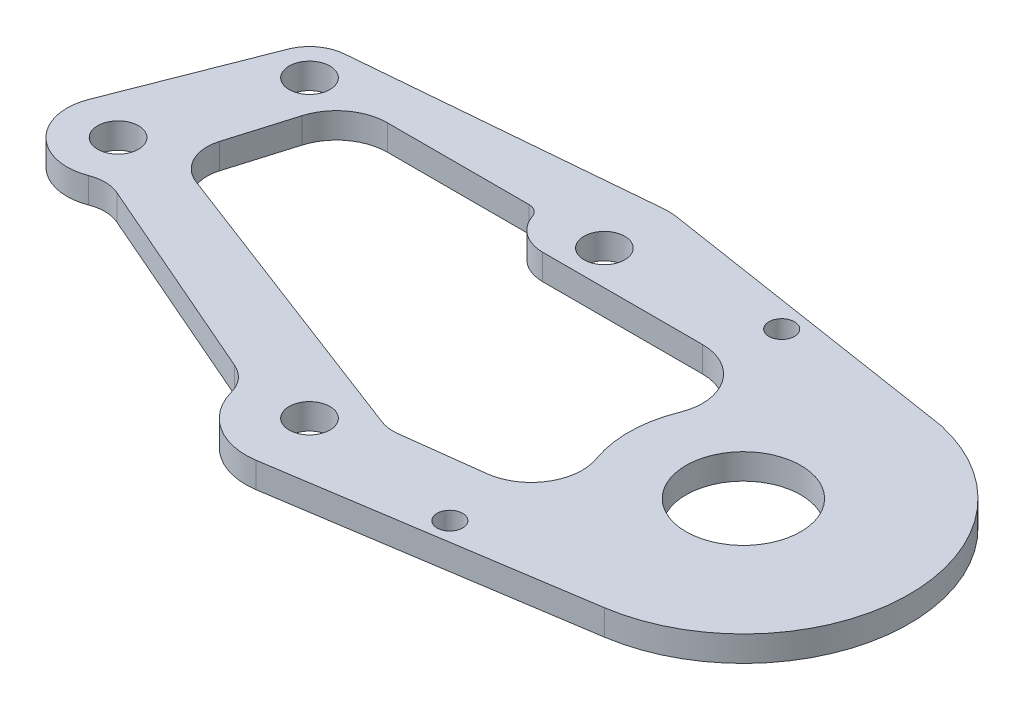
SolidWorks part; units mm, degrees
ref_plane "Front Plane" through (0, 0, 0) normal (0, 0, 1) x (1, 0, 0)
ref_plane "Top Plane" through (0, 0, 0) normal (0, 1, 0) x (1, 0, 0)
ref_plane "Right Plane" through (0, 0, 0) normal (1, 0, 0) x (0, 0, -1)
sketch "Sketch1" plane through (0, 0, 0) normal (0, 1, 0) x (1, 0, 0)
  line L1 (35.9792, -12.8485) -> (12.3136, -16.494)
  line L3 (36.8136, 12.6919) -> (12.3191, 16.493)
  line L5 (11.1196, 16.5334) -> (-11.812, 14.5411)
  line L7 (-14.2449, 12.8753) -> (-19.4876, 2.2049)
  line L9 (-16.9948, -4.5849) -> (9.5576, -16.1371)
  circle A0 centre (0, 0) radius 5.5
  circle A9 centre (-15, 0) radius 1.6
  circle A12 centre (14, 0) radius 4.5
  circle A20 centre (25, 11) radius 1
  circle A21 centre (25, -11) radius 1
  circle A23 centre (34, 0) radius 4.5
  circle A24 centre (-11.5524, 11.5524) radius 1.6
  circle A25 centre (11.5523, 11.5522) radius 1.6
  circle A26 centre (11.5523, -11.5523) radius 1.6
  arc A33 (12.3191, 16.493) -> (11.1196, 16.5334) centre (11.5523, 11.5522) ccw
  arc A34 (-11.812, 14.5411) -> (-14.2449, 12.8753) centre (-11.5524, 11.5524) ccw
  arc A35 (-19.4876, 2.2049) -> (-16.9948, -4.5849) centre (-15, 0) ccw
  arc A36 (9.5576, -16.1371) -> (12.3136, -16.494) centre (11.5523, -11.5523) ccw
  arc A37 (35.9792, -12.8485) -> (35.1652, 12.9477) centre (34, 0) ccw
extrude "Boss-Extrude2" add sketch "Sketch1" along normal blind 2 contours L1 A37 L3 A33 L5 A34 L7 A35 L9 A36 A0 A9 A12 A20 A21 A23 A24 A25 A26
sketch "Sketch2" plane through (0, 2, 0) normal (0, 1, 0) x (1, 0, 0)
  circle A0 centre (25, 11) radius 1
  circle A1 centre (25, -11) radius 1
extrude "Boss-Extrude3" add sketch "Sketch2" against normal up to surface (2 mm away) up to face at (0, 0, 5.5)
sketch "Sketch3" plane through (0, 2, 0) normal (0, 1, 0) x (1, 0, 0)
  circle A0 centre (24, 13) radius 1
  circle A1 centre (24, -13) radius 1
extrude "Cut-Extrude1" cut sketch "Sketch3" against normal blind 103
sketch "Sketch4" plane through (0, 2, 0) normal (0, 1, 0) x (1, 0, 0)
  line L0 (-11.5562, 1.049) -> (-9.2694, 8.7117)
  line L1 (-9.2694, 8.7117) -> (11.5178, 8.4785)
  line L2 (-11.5562, 1.049) -> (11.5464, -7.7739)
  line L4 (11.5464, -7.7739) -> (15.2588, -9.1916)
  line L5 (11.5178, 8.4785) -> (14.721, 8.4426)
  arc A6 (15.2588, -9.1916) -> (14.721, 8.4426) centre (14.9899, -0.3745) ccw
extrude "Cut-Extrude2" cut sketch "Sketch4" against normal blind 10
sketch "Sketch5" plane through (0, 2, 0) normal (0, 1, 0) x (1, 0, 0)
  line L0 (-5.3378, -1.3258) -> (3.0952, -4.5464)
  line L1 (3.0952, -4.5464) -> (3.756, -8.1059)
  line L2 (3.756, -8.1059) -> (-7.7705, -5.6439)
  line L3 (-7.7705, -5.6439) -> (-5.3378, -1.3258)
extrude "Boss-Extrude4" add sketch "Sketch5" against normal up to surface (2 mm away) up to face at (2.4813, 0, -0.201)
fillet "Fillet1" radius 3 4 edges at (14.721, 1, -8.4426) (15.2588, 1, 9.1916) (-9.2694, 1, -8.7117) (-11.5562, 1, -1.049)
sketch "Sketch6" plane through (0, 2, 0) normal (0, 1, 0) x (1, 0, 0)
  line L0 (-10.4151, -1.9948) -> (6.9675, -9.5575)
  line L2 (-16.9948, -4.5849) -> (-19.442, -14.3186)
  line L3 (-19.442, -14.3186) -> (4.6402, -19.6259)
  line L4 (4.6402, -19.6259) -> (11.5523, -16.5523)
  arc A0 (-16.9948, -4.5849) -> (-10.4151, -1.9948) centre (-15, 0) ccw
  arc A1 (6.9675, -9.5575) -> (11.5523, -16.5523) centre (11.5523, -11.5523) ccw
extrude "Cut-Extrude3" cut sketch "Sketch6" against normal blind 10
sketch "Sketch7" plane through (0, 2, 0) normal (0, 1, 0) x (1, 0, 0)
  line L0 (-14.346, 12.6458) -> (-18.7249, 1.4579)
  line L1 (-15, 0) -> (-5.5378, -4.1168)
  line L2 (6.9675, -9.5575) -> (-10.4151, -1.9948) construction
  line L3 (-5.5378, -4.1168) -> (-13.6864, -14.8926)
  line L4 (-13.6864, -14.8926) -> (-40.0279, 1.7466)
  line L5 (-40.0279, 1.7466) -> (-14.346, 12.6458)
  circle A0 centre (-15, 0) radius 4
  circle A1 centre (-11.5524, 11.5524) radius 3
  line M1 (-10.4151, -1.9948) -> (6.9675, -9.5575)
  line M9 (-14.2449, 12.8753) -> (-19.4876, 2.2049)
  arc M10 (-19.4876, 2.2049) -> (-10.4151, -1.9948) centre (-15, 0) ccw
extrude "Cut-Extrude4" cut sketch "Sketch7" against normal blind 10 contours L5 L4 L3 M1 M10 M9 | A0 L0 L5 L1 M9 M10
sketch "Sketch8" plane through (0, 2, 0) normal (0, 1, 0) x (1, 0, 0)
  line L2 (-2.5813, -6.4936) -> (8.3236, -11.2381)
  line L3 (8.3236, -11.2381) -> (9.1528, -8.1373)
  line L4 (9.1528, -8.1373) -> (-12.0054, 0)
  line L5 (-12.0054, 0) -> (-12.794, -2.0503)
  line L6 (-12.794, -2.0503) -> (-2.5813, -6.4936)
extrude "Boss-Extrude5" add sketch "Sketch8" against normal up to surface (2 mm away) up to face at (11.5523, 0, 13.1523)
sketch "Sketch9" plane through (0, 2, 0) normal (0, 1, 0) x (1, 0, 0)
  line L0 (3.8276, 8.5648) -> (30.4406, 8.2662)
  line L1 (14.663, 8.4432) -> (-7.0078, 8.6863) construction
  line L2 (16.0763, -9.1286) -> (29.0526, -7.5182)
  line L3 (3.8276, 8.5648) -> (16.0763, -9.1286)
  arc A0 (30.4406, 8.2662) -> (29.0526, -7.5182) centre (34, 0) ccw
extrude "Cut-Extrude5" cut sketch "Sketch9" against normal blind 10
sketch "Sketch10" plane through (0, 2, 0) normal (0, 1, 0) x (1, 0, 0)
  line L6 (-9.9162, 6.5444) -> (25.0224, -0.6346)
  line L7 (22.9485, 8.3503) -> (22.9485, 8.8503)
  line L9 (30.4406, 8.2662) -> (15.4565, 8.4343) construction
  line L10 (22.9485, 8.8503) -> (32.3651, 8.8503)
  line L11 (32.3651, 8.8503) -> (-9.4424, 8.8503)
  line L12 (-9.9162, 6.5444) -> (-9.4424, 8.8503)
  arc A1 (30.4406, 8.2662) -> (29.0526, -7.5182) centre (34, 0) ccw construction
  arc A4 (32.3651, 8.8503) -> (25.0224, -0.6346) centre (34, 0) ccw
  line M4 (15.4565, 8.4343) -> (30.4406, 8.2662)
  arc M5 (30.4406, 8.2662) -> (29.0526, -7.5182) centre (34, 0) ccw
  arc M11 (-9.9162, 6.5444) -> (-7.0078, 8.6863) centre (-7.0414, 5.6865) cw
  line M12 (-7.0078, 8.6863) -> (14.663, 8.4432)
  arc M13 (14.663, 8.4432) -> (14.7711, 8.4439) centre (14.6967, 11.443) ccw
  arc M14 (14.7711, 8.4439) -> (15.4565, 8.4343) centre (14.9899, -0.3745) cw
extrude "Cut-Extrude9" cut sketch "Sketch10" against normal blind 10 contours L6 M11 M5 M4 M14 M13 M12 | L12 L7 L11 M11 M12 M13 M14 M4 | A4 L10 L7 M4
fillet "Fillet3" radius 4 3 edges at (-9.4424, 1, -8.8503) (32.3651, 1, -8.8503) (29.0526, 1, 7.5182)
sketch "Sketch11" plane through (0, 2, 0) normal (0, 1, 0) x (1, 0, 0)
  line L0 (-10.7602, 3.7163) -> (-8.4217, 11.5522)
  line L1 (6.5523, 11.5522) -> (-8.4217, 11.5522)
  line L2 (11.5523, 6.5522) -> (-10.7602, 3.7163)
  circle A0 centre (11.5523, 11.5522) radius 5
  line M23 (-6.2474, 8.8503) -> (21.9387, 8.8503)
  arc M32 (-10.0804, 5.9942) -> (-6.2474, 8.8503) centre (-6.2474, 4.8503) cw
extrude "Cut-Extrude10" cut sketch "Sketch11" against normal blind 10 contours A0 L1 L0 M32 M23
fillet "Fillet4" radius 4 1 edges at (-8.4217, 1, -11.5522)
fillet "Fillet6" radius 1 1 edges at (6.5523, 1, -11.5522)
fillet "Fillet7" radius 3 1 edges at (7.3452, 1, -8.8503)
sketch "Sketch13" plane through (0, 2, 0) normal (0, 1, 0) x (1, 0, 0)
  line L0 (-2.5932, -6.4885) -> (-2.9921, -7.4054)
  line L1 (-11.8475, -2.4621) -> (6.6612, -10.5148) construction
  line L2 (-2.9921, -7.4054) -> (7.9609, -12.1708)
  line L3 (-2.9921, -7.4054) -> (-13.9219, -2.6501)
  line L4 (-13.9219, -2.6501) -> (-12.2111, -0.3296)
  line L5 (-12.2111, -0.3296) -> (7.9609, -9.7881)
  line L6 (7.9609, -9.7881) -> (7.9609, -12.1708)
  arc M2 (-18.7249, 1.4579) -> (-11.8475, -2.4621) centre (-15, 0) ccw
  line M3 (-11.8475, -2.4621) -> (6.6612, -10.5148)
  arc M4 (6.6612, -10.5148) -> (12.3136, -16.494) centre (11.5523, -11.5523) ccw
  line M5 (12.3136, -16.494) -> (35.9792, -12.8485)
  arc M6 (35.9792, -12.8485) -> (36.8136, 12.6919) centre (34, 0) ccw
  line M7 (36.8136, 12.6919) -> (12.3191, 16.493)
  arc M8 (12.3191, 16.493) -> (11.1196, 16.5334) centre (11.5523, 11.5522) ccw
  line M9 (11.1196, 16.5334) -> (-11.812, 14.5411)
  arc M10 (-11.812, 14.5411) -> (-14.2449, 12.8753) centre (-11.5524, 11.5524) ccw
  line M11 (-14.2449, 12.8753) -> (-14.3608, 12.6395)
  line M12 (-14.3608, 12.6395) -> (-14.346, 12.6458)
  line M13 (-14.346, 12.6458) -> (-18.7249, 1.4579)
  circle M14 centre (24, 13) radius 1
  circle M15 centre (24, -13) radius 1
  circle M16 centre (-15, 0) radius 1.6
  circle M17 centre (34, 0) radius 4.5
  circle M18 centre (-11.5524, 11.5524) radius 1.6
  circle M19 centre (11.5523, 11.5522) radius 1.6
  circle M20 centre (11.5523, -11.5523) radius 1.6
  arc M21 (5.6362, 11.5522) -> (6.5821, 10.8767) centre (5.6362, 10.5522) cw
  arc M22 (6.5821, 10.8767) -> (9.4198, 8.8503) centre (9.4198, 11.8503) ccw
  line M23 (9.4198, 8.8503) -> (21.9387, 8.8503)
  arc M24 (21.9387, 8.8503) -> (25.6499, 3.3579) centre (21.9387, 4.8503) cw
  arc M25 (25.6499, 3.3579) -> (25.5292, -3.0406) centre (34, 0) ccw
  arc M26 (25.5292, -3.0406) -> (22.257, -8.3615) centre (21.7644, -4.392) cw
  line M27 (22.257, -8.3615) -> (16.0763, -9.1286)
  arc M28 (16.0763, -9.1286) -> (14.6365, -8.954) centre (15.7068, -6.1514) cw
  line M29 (14.6365, -8.954) -> (-8.9557, 0.0558)
  arc M30 (-8.9557, 0.0558) -> (-10.7602, 3.7163) centre (-7.8854, 2.8584) cw
  line M31 (-10.7602, 3.7163) -> (-9.274, 8.6961)
  arc M32 (-9.274, 8.6961) -> (-5.4411, 11.5522) centre (-5.4411, 7.5522) cw
  line M33 (-5.4411, 11.5522) -> (5.6362, 11.5522)
extrude "Boss-Extrude7" add sketch "Sketch13" against normal up to surface (2 mm away) contours L3 L0 M3 M2 | L0 L2 M4 M3 | L5 L6 L2 L3 L4 M4 M5 M6 M7 M8 M9 M10 M11 M12 M13 M2 M14 M16 M18 M20 M33 M21 M22 M23 M24 M25 M26 M27 M28 M29 M30 M31 M32 M19 M17 M15 up to face at (3.0822, 0, -4.426)
fillet "Fillet8" radius 3 2 edges at (6.5524, 1, 11.558) (-12.6214, 1, 3.216)
